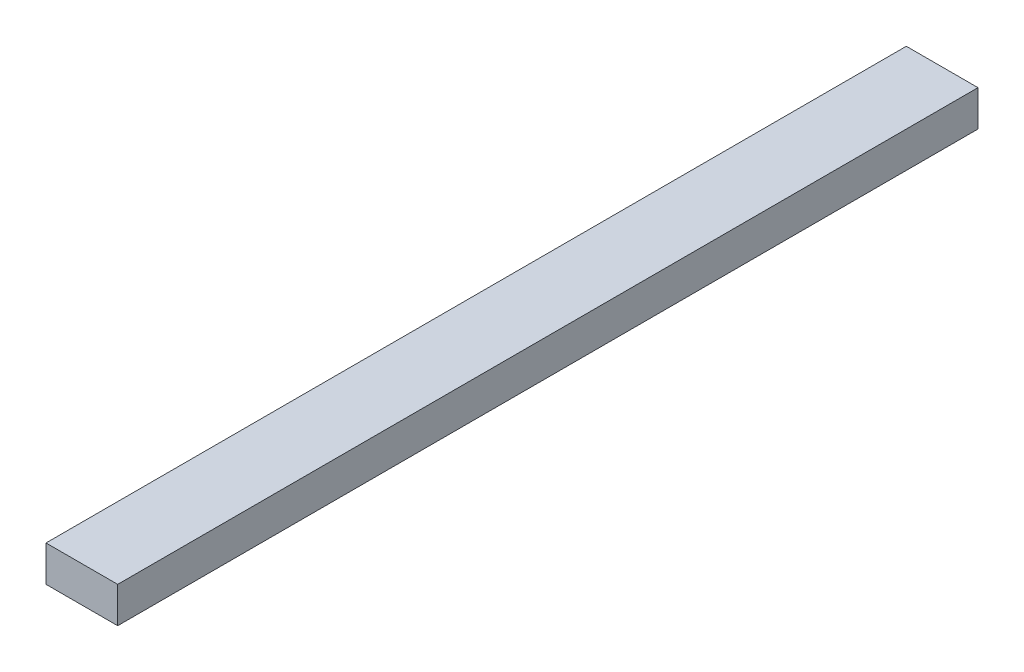
SolidWorks part; units mm, degrees
ref_plane "Front Plane" through (0, 0, 0) normal (0, 0, 1) x (1, 0, 0)
ref_plane "Top Plane" through (0, 0, 0) normal (0, 1, 0) x (1, 0, 0)
ref_plane "Right Plane" through (0, 0, 0) normal (1, 0, 0) x (0, 0, -1)
sketch "Sketch1" plane through (0, 0, 0) normal (0, 0, 1) x (1, 0, 0)
  line L1 (0, 0) -> (50.8, 0)
  line L2 (0, 0) -> (0, 25.4)
  line L3 (0, 25.4) -> (50.8, 25.4)
  line L4 (50.8, 0) -> (50.8, 25.4)
  dimension "D1" = 25.4
  dimension "D2" = 50.8
extrude "Boss-Extrude1" add sketch "Sketch1" along normal blind 609.6
